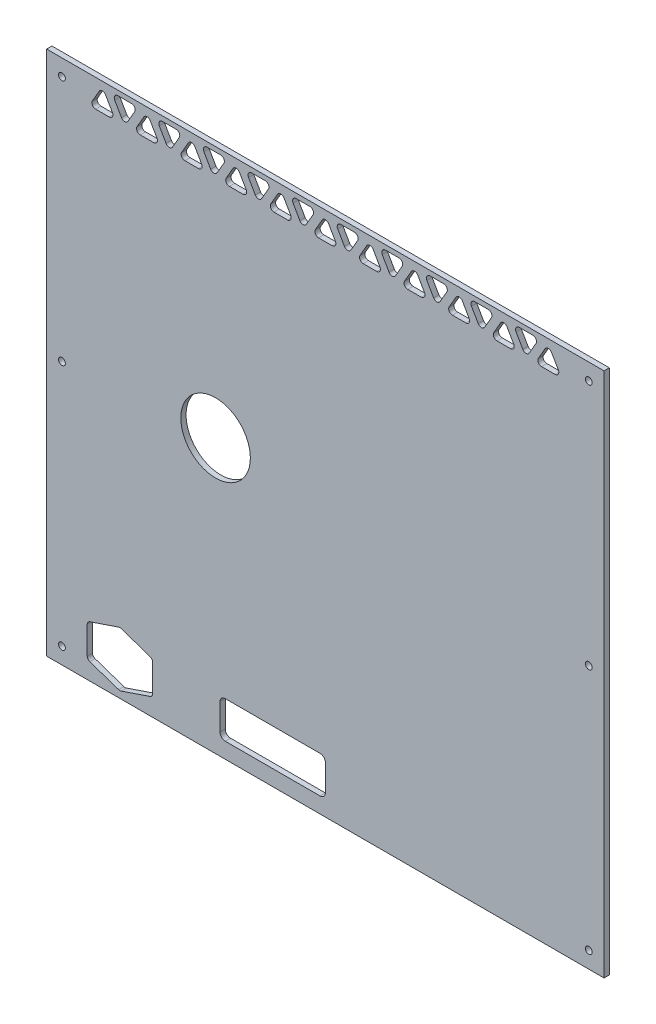
SolidWorks part; units mm, degrees
material "Acrylic (Medium-high impact)"
ref_plane "Front Plane" through (0, 0, 0) normal (0, 0, 1) x (1, 0, 0)
ref_plane "Top Plane" through (0, 0, 0) normal (0, 1, 0) x (1, 0, 0)
ref_plane "Right Plane" through (0, 0, 0) normal (1, 0, 0) x (0, 0, -1)
sketch "Model" plane through (0, 0, 0) normal (0, 0, 1) x (1, 0, 0)
  line L0 (80.4979, 494.5) -> (67.6222, 494.5)
  line L1 (64.5911, 489.25) -> (71.029, 478.0994)
  line L2 (77.0911, 478.0994) -> (83.529, 489.25)
  line L3 (62.3689, 478.099) -> (55.9311, 489.2496)
  line L4 (49.8689, 489.2496) -> (43.4311, 478.099)
  line L5 (46.4622, 472.849) -> (59.3378, 472.849)
  line L6 (104.689, 478.099) -> (98.2512, 489.2496)
  line L7 (92.189, 489.2496) -> (85.7512, 478.099)
  line L8 (88.7823, 472.849) -> (101.6579, 472.849)
  line L9 (147.0091, 478.099) -> (140.5713, 489.2496)
  line L10 (134.5091, 489.2496) -> (128.0713, 478.099)
  line L11 (131.1024, 472.849) -> (143.978, 472.849)
  line L12 (189.3292, 478.099) -> (182.8913, 489.2496)
  line L13 (176.8292, 489.2496) -> (170.3913, 478.099)
  line L14 (173.4224, 472.849) -> (186.2981, 472.849)
  line L15 (231.6493, 478.099) -> (225.2114, 489.2496)
  line L16 (219.1493, 489.2496) -> (212.7114, 478.099)
  line L17 (215.7425, 472.849) -> (228.6182, 472.849)
  line L18 (273.9693, 478.099) -> (267.5315, 489.2496)
  line L19 (261.4693, 489.2496) -> (255.0315, 478.099)
  line L20 (258.0626, 472.849) -> (270.9383, 472.849)
  line L21 (316.2894, 478.099) -> (309.8516, 489.2496)
  line L22 (303.7894, 489.2496) -> (297.3516, 478.099)
  line L23 (300.3827, 472.849) -> (313.2583, 472.849)
  line L24 (358.6095, 478.099) -> (352.1717, 489.2496)
  line L25 (346.1095, 489.2496) -> (339.6717, 478.099)
  line L26 (342.7028, 472.849) -> (355.5784, 472.849)
  line L27 (400.9296, 478.099) -> (394.4918, 489.2496)
  line L28 (388.4296, 489.2496) -> (381.9918, 478.099)
  line L29 (385.0229, 472.849) -> (397.8985, 472.849)
  line L30 (443.2497, 478.099) -> (436.8119, 489.2496)
  line L31 (430.7497, 489.2496) -> (424.3119, 478.099)
  line L32 (427.343, 472.849) -> (440.2186, 472.849)
  line L33 (485.5698, 478.099) -> (479.132, 489.2496)
  line L34 (473.0698, 489.2496) -> (466.632, 478.099)
  line L35 (469.663, 472.849) -> (482.5387, 472.849)
  line L36 (62.3689, 478.099) -> (104.689, 478.099) construction
  line L37 (122.818, 494.5) -> (109.9423, 494.5)
  line L38 (106.9112, 489.25) -> (113.349, 478.0994)
  line L39 (119.4112, 478.0994) -> (125.849, 489.25)
  line L40 (165.138, 494.5) -> (152.2624, 494.5)
  line L41 (149.2313, 489.25) -> (155.6691, 478.0994)
  line L42 (161.7313, 478.0994) -> (168.1691, 489.25)
  line L43 (207.4581, 494.5) -> (194.5825, 494.5)
  line L44 (191.5514, 489.25) -> (197.9892, 478.0994)
  line L45 (204.0514, 478.0994) -> (210.4892, 489.25)
  line L46 (249.7782, 494.5) -> (236.9026, 494.5)
  line L47 (233.8715, 489.25) -> (240.3093, 478.0994)
  line L48 (246.3715, 478.0994) -> (252.8093, 489.25)
  line L49 (292.0983, 494.5) -> (279.2227, 494.5)
  line L50 (276.1916, 489.25) -> (282.6294, 478.0994)
  line L51 (100.4996, 45.4248) -> (100.4996, 19.2924)
  line L52 (98.1233, 15.9777) -> (70.6233, 6.6557)
  line L53 (68.376, 6.6557) -> (40.876, 15.9777)
  line L54 (38.4996, 19.2924) -> (38.4996, 45.4248)
  line L55 (40.876, 48.7395) -> (68.376, 58.0616)
  line L56 (70.6233, 58.0616) -> (98.1233, 48.7395)
  line L57 (288.6916, 478.0994) -> (295.1294, 489.25)
  line L58 (334.4184, 494.5) -> (321.5427, 494.5)
  line L59 (318.5117, 489.25) -> (324.9495, 478.0994)
  line L60 (331.0117, 478.0994) -> (337.4495, 489.25)
  line L61 (376.7385, 494.5) -> (363.8628, 494.5)
  line L62 (360.8317, 489.25) -> (367.2696, 478.0994)
  line L63 (373.3317, 478.0994) -> (379.7696, 489.25)
  line L64 (419.0586, 494.5) -> (406.1829, 494.5)
  line L65 (403.1518, 489.25) -> (409.5896, 478.0994)
  line L66 (415.6518, 478.0994) -> (422.0896, 489.25)
  line L67 (461.3786, 494.5) -> (448.503, 494.5)
  line L68 (445.4719, 489.25) -> (451.9097, 478.0994)
  line L69 (529, 499) -> (529, 0)
  line L70 (529, 0) -> (0, 0)
  line L71 (0, 0) -> (0, 499)
  line L72 (0, 499) -> (529, 499)
  line L73 (264.5, 44.8586) -> (264.5, 19.8586)
  line L74 (164.5, 19.8586) -> (164.5, 44.8586)
  line L75 (169.5, 49.8586) -> (259.5, 49.8586)
  line L76 (457.9719, 478.0994) -> (464.4097, 489.25)
  line L77 (80.4979, 494.5) -> (122.818, 494.5) construction
  line L78 (259.5, 14.8586) -> (169.5, 14.8586)
  circle A0 centre (514.5, 483.5) radius 3.25
  circle A1 centre (514.5, 249.5) radius 3.25
  circle A2 centre (14.5, 249.5) radius 3.25
  circle A3 centre (514.5, 15.5) radius 3.25
  circle A4 centre (14.5, 483.5) radius 3.25
  circle A5 centre (14.5, 15.5) radius 3.25
  arc A6 (264.5, 44.8586) -> (259.5, 49.8586) centre (259.5, 44.8586) ccw
  arc A7 (259.5, 14.8586) -> (264.5, 19.8586) centre (259.5, 19.8586) ccw
  arc A8 (164.5, 19.8586) -> (169.5, 14.8586) centre (169.5, 19.8586) ccw
  arc A9 (169.5, 49.8586) -> (164.5, 44.8586) centre (169.5, 44.8586) ccw
  arc A10 (98.2512, 489.2496) -> (92.189, 489.2496) centre (95.2201, 487.4996) ccw
  circle A11 centre (160.3, 259.55) radius 33
  arc A12 (67.6222, 494.5) -> (64.5911, 489.25) centre (67.6222, 491) ccw
  arc A13 (71.029, 478.0994) -> (77.0911, 478.0994) centre (74.06, 479.8494) ccw
  arc A14 (83.529, 489.25) -> (80.4979, 494.5) centre (80.4979, 491) ccw
  arc A15 (55.9311, 489.2496) -> (49.8689, 489.2496) centre (52.9, 487.4996) ccw
  arc A16 (43.4311, 478.099) -> (46.4622, 472.849) centre (46.4622, 476.349) ccw
  arc A17 (59.3378, 472.849) -> (62.3689, 478.099) centre (59.3378, 476.349) ccw
  arc A18 (85.7512, 478.099) -> (88.7823, 472.849) centre (88.7823, 476.349) ccw
  arc A19 (101.6579, 472.849) -> (104.689, 478.099) centre (101.6579, 476.349) ccw
  arc A20 (140.5713, 489.2496) -> (134.5091, 489.2496) centre (137.5402, 487.4996) ccw
  arc A21 (128.0713, 478.099) -> (131.1024, 472.849) centre (131.1024, 476.349) ccw
  arc A22 (143.978, 472.849) -> (147.0091, 478.099) centre (143.978, 476.349) ccw
  arc A23 (182.8913, 489.2496) -> (176.8292, 489.2496) centre (179.8603, 487.4996) ccw
  arc A24 (170.3913, 478.099) -> (173.4224, 472.849) centre (173.4224, 476.349) ccw
  arc A25 (186.2981, 472.849) -> (189.3292, 478.099) centre (186.2981, 476.349) ccw
  arc A26 (225.2114, 489.2496) -> (219.1493, 489.2496) centre (222.1803, 487.4996) ccw
  arc A27 (212.7114, 478.099) -> (215.7425, 472.849) centre (215.7425, 476.349) ccw
  arc A28 (228.6182, 472.849) -> (231.6493, 478.099) centre (228.6182, 476.349) ccw
  arc A29 (267.5315, 489.2496) -> (261.4693, 489.2496) centre (264.5004, 487.4996) ccw
  arc A30 (255.0315, 478.099) -> (258.0626, 472.849) centre (258.0626, 476.349) ccw
  arc A31 (270.9383, 472.849) -> (273.9693, 478.099) centre (270.9383, 476.349) ccw
  arc A32 (309.8516, 489.2496) -> (303.7894, 489.2496) centre (306.8205, 487.4996) ccw
  arc A33 (297.3516, 478.099) -> (300.3827, 472.849) centre (300.3827, 476.349) ccw
  arc A34 (313.2583, 472.849) -> (316.2894, 478.099) centre (313.2583, 476.349) ccw
  arc A35 (352.1717, 489.2496) -> (346.1095, 489.2496) centre (349.1406, 487.4996) ccw
  arc A36 (339.6717, 478.099) -> (342.7028, 472.849) centre (342.7028, 476.349) ccw
  arc A37 (355.5784, 472.849) -> (358.6095, 478.099) centre (355.5784, 476.349) ccw
  arc A38 (394.4918, 489.2496) -> (388.4296, 489.2496) centre (391.4607, 487.4996) ccw
  arc A39 (381.9918, 478.099) -> (385.0229, 472.849) centre (385.0229, 476.349) ccw
  arc A40 (397.8985, 472.849) -> (400.9296, 478.099) centre (397.8985, 476.349) ccw
  arc A41 (436.8119, 489.2496) -> (430.7497, 489.2496) centre (433.7808, 487.4996) ccw
  arc A42 (424.3119, 478.099) -> (427.343, 472.849) centre (427.343, 476.349) ccw
  arc A43 (440.2186, 472.849) -> (443.2497, 478.099) centre (440.2186, 476.349) ccw
  arc A44 (479.132, 489.2496) -> (473.0698, 489.2496) centre (476.1009, 487.4996) ccw
  arc A45 (466.632, 478.099) -> (469.663, 472.849) centre (469.663, 476.349) ccw
  arc A46 (482.5387, 472.849) -> (485.5698, 478.099) centre (482.5387, 476.349) ccw
  arc A47 (109.9423, 494.5) -> (106.9112, 489.25) centre (109.9423, 491) ccw
  arc A48 (113.349, 478.0994) -> (119.4112, 478.0994) centre (116.3801, 479.8494) ccw
  arc A49 (125.849, 489.25) -> (122.818, 494.5) centre (122.818, 491) ccw
  arc A50 (152.2624, 494.5) -> (149.2313, 489.25) centre (152.2624, 491) ccw
  arc A51 (155.6691, 478.0994) -> (161.7313, 478.0994) centre (158.7002, 479.8494) ccw
  arc A52 (168.1691, 489.25) -> (165.138, 494.5) centre (165.138, 491) ccw
  arc A53 (194.5825, 494.5) -> (191.5514, 489.25) centre (194.5825, 491) ccw
  arc A54 (197.9892, 478.0994) -> (204.0514, 478.0994) centre (201.0203, 479.8494) ccw
  arc A55 (210.4892, 489.25) -> (207.4581, 494.5) centre (207.4581, 491) ccw
  arc A56 (236.9026, 494.5) -> (233.8715, 489.25) centre (236.9026, 491) ccw
  arc A57 (240.3093, 478.0994) -> (246.3715, 478.0994) centre (243.3404, 479.8494) ccw
  arc A58 (252.8093, 489.25) -> (249.7782, 494.5) centre (249.7782, 491) ccw
  arc A59 (279.2227, 494.5) -> (276.1916, 489.25) centre (279.2227, 491) ccw
  arc A60 (282.6294, 478.0994) -> (288.6916, 478.0994) centre (285.6605, 479.8494) ccw
  arc A61 (295.1294, 489.25) -> (292.0983, 494.5) centre (292.0983, 491) ccw
  arc A62 (321.5427, 494.5) -> (318.5117, 489.25) centre (321.5427, 491) ccw
  arc A63 (100.4996, 45.4248) -> (98.1233, 48.7395) centre (96.9996, 45.4248) ccw
  arc A64 (98.1233, 15.9777) -> (100.4996, 19.2924) centre (96.9996, 19.2924) ccw
  arc A65 (68.376, 6.6557) -> (70.6233, 6.6557) centre (69.4996, 9.9704) ccw
  arc A66 (38.4996, 19.2924) -> (40.876, 15.9777) centre (41.9996, 19.2924) ccw
  arc A67 (40.876, 48.7395) -> (38.4996, 45.4248) centre (41.9996, 45.4248) ccw
  arc A68 (70.6233, 58.0616) -> (68.376, 58.0616) centre (69.4996, 54.7468) ccw
  arc A69 (324.9495, 478.0994) -> (331.0117, 478.0994) centre (327.9806, 479.8494) ccw
  arc A70 (337.4495, 489.25) -> (334.4184, 494.5) centre (334.4184, 491) ccw
  arc A71 (363.8628, 494.5) -> (360.8317, 489.25) centre (363.8628, 491) ccw
  arc A72 (367.2696, 478.0994) -> (373.3317, 478.0994) centre (370.3006, 479.8494) ccw
  arc A73 (379.7696, 489.25) -> (376.7385, 494.5) centre (376.7385, 491) ccw
  arc A74 (406.1829, 494.5) -> (403.1518, 489.25) centre (406.1829, 491) ccw
  arc A75 (409.5896, 478.0994) -> (415.6518, 478.0994) centre (412.6207, 479.8494) ccw
  arc A76 (422.0896, 489.25) -> (419.0586, 494.5) centre (419.0586, 491) ccw
  arc A77 (448.503, 494.5) -> (445.4719, 489.25) centre (448.503, 491) ccw
  arc A78 (451.9097, 478.0994) -> (457.9719, 478.0994) centre (454.9408, 479.8494) ccw
  arc A79 (464.4097, 489.25) -> (461.3786, 494.5) centre (461.3786, 491) ccw
  dimension "D5" = 6.5
  dimension "D6" = 14.5
  dimension "D7" = 249.5
  dimension "D8" = 483.5
  dimension "D9" = 66
  dimension "D14" = 5
  dimension "D28" = 3.5
  dimension "D1" = 529
  dimension "D2" = 499
  dimension "D3" = 15.5
  dimension "D4" = 14.5
  dimension "D10" = 259.55
  dimension "D11" = 160.3
  dimension "D12" = 35
  dimension "D13" = 100
  dimension "D15" = 14.8586
  dimension "D16" = 164.5
  dimension "D17" = 9.9704
  dimension "D18" = 69.4996
  dimension "D19" = 27.5
  dimension "D20" = 27.5
  dimension "D21" = 26.1324
  dimension "D22" = 44.7764
  dimension "D23" = 11.5004
  dimension "D24" = 52.9
  dimension "D25" = 11
  dimension "D26" = 12.8756
  dimension "D27" = 21.16
  dimension "D29" = 19.1506
  dimension "D30" = 42.3201
  dimension "D31" = 10
  dimension "D32" = 42.3201
extrude "Boss-Extrude1" add sketch "Model" along normal blind 5
